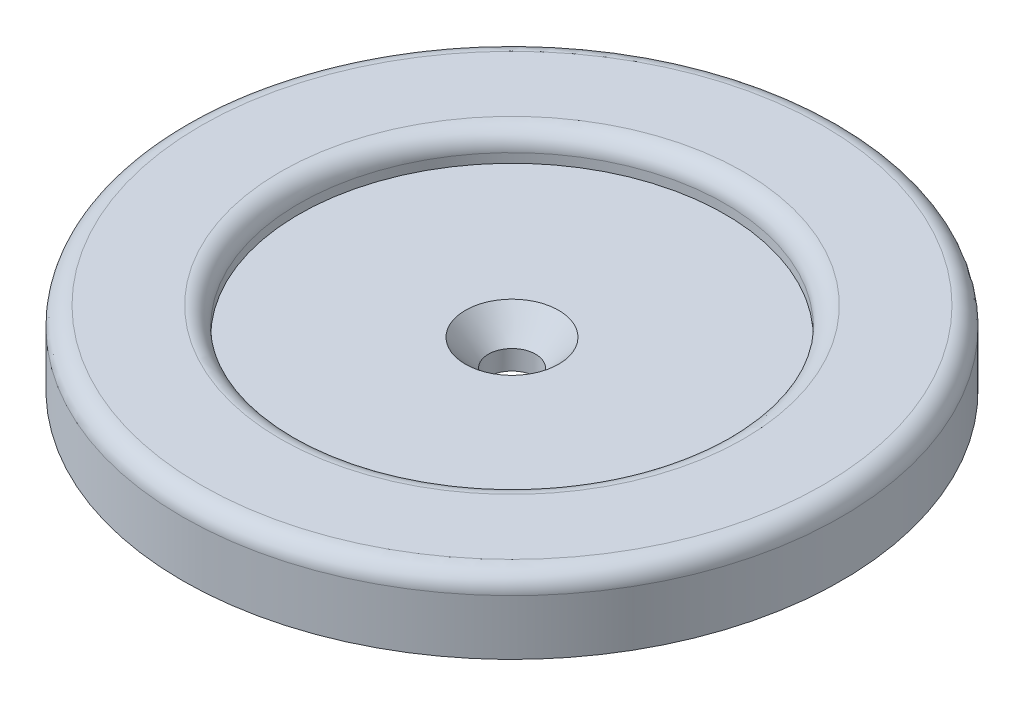
SolidWorks part; units mm, degrees
ref_plane "Front Plane" through (0, 0, 0) normal (0, 0, 1) x (1, 0, 0)
ref_plane "Top Plane" through (0, 0, 0) normal (0, 1, 0) x (1, 0, 0)
ref_plane "Right Plane" through (0, 0, 0) normal (1, 0, 0) x (0, 0, -1)
sketch "Sketch1" plane through (0, 0, 0) normal (0, 1, 0) x (1, 0, 0)
  circle A0 centre (0, 0) radius 20.066 construction
  circle A1 centre (0, 0) radius 45.466
  dimension "D1" = 25.4
extrude "Boss-Extrude1" add sketch "Sketch1" along normal blind 25.4
sketch "Sketch3" plane through (0, 0, 0) normal (0, -1, 0) x (1, 0, 0)
  circle A0 centre (0, 0) radius 20.32
hole_wizard "CSK for 1/4 Flat Head Machine Screw1" positions "Sketch6" profile "Sketch7" countersink size "1/4" standard "ANSI Inch"
sketch "Sketch6" plane through (0, 25.4, 0) normal (0, 1, 0) x (1, 0, 0)
  point P0 (0, 0)
sketch "Sketch7" plane through (0, 25.4, 0) normal (1, 0, 0) x (0, 0, 1)
  line L0 (0, 0) -> (0, 27.3611)
  line L1 (0, 27.3611) -> (3.2639, 25.4)
  line L2 (3.2639, 25.4) -> (3.2639, 3.6524)
  line L3 (3.2639, 3.6524) -> (6.4389, 0)
  line L5 (6.4389, 0) -> (0, 0)
  line L6 (-3.2639, 3.6524) -> (-6.4389, 0) construction
  line L10 (0, 27.3611) -> (-3.2639, 25.4) construction
  line L11 (0, -6.35) -> (0, 107.95) construction
  dimension "Hole Dia." = 6.5278
  dimension "Hole Depth" = 25.4
  dimension "Near C'Sink Dia." = 12.8778
  dimension "Near C'Sink Angle" = 82
  dimension "Drill Angle" = 118
sketch "Sketch9" plane through (0, 0, 0) normal (0, -1, 0) x (1, 0, 0)
  circle A0 centre (0, 0) radius 53.0319
extrude "Cut-Extrude3" cut sketch "Sketch9" against normal blind 12.7
sketch "Sketch11" plane through (0, 12.7, 0) normal (0, -1, 0) x (1, 0, 0)
  circle A0 centre (0, 0) radius 48.964
extrude "Cut-Extrude4" cut sketch "Sketch11" against normal blind 6.35
sketch "Sketch13" plane through (0, 25.4, 0) normal (0, 1, 0) x (1, 0, 0)
  circle A0 centre (0, 0) radius 29.3982
  circle A1 centre (0, 0) radius 45.466
extrude "Boss-Extrude2" add sketch "Sketch13" along normal blind 3.81
sketch "Sketch12" plane through (0, 19.05, 0) normal (0, -1, 0) x (1, 0, 0)
  circle A0 centre (0, 0) radius 38.3099 construction
  circle A1 centre (0, 38.3099) radius 3.1309
  circle A2 centre (9.9153, 37.0045) radius 3.1309
  circle A3 centre (19.1549, 33.1773) radius 3.1309
  circle A4 centre (27.0892, 27.0892) radius 3.1309
  circle A5 centre (33.1773, 19.1549) radius 3.1309
  circle A6 centre (37.0045, 9.9153) radius 3.1309
  circle A7 centre (38.3099, 0) radius 3.1309
  circle A8 centre (37.0045, -9.9153) radius 3.1309
  circle A9 centre (33.1773, -19.1549) radius 3.1309
  circle A10 centre (27.0892, -27.0892) radius 3.1309
  circle A11 centre (19.1549, -33.1773) radius 3.1309
  circle A12 centre (9.9153, -37.0045) radius 3.1309
  circle A13 centre (0, -38.3099) radius 3.1309
  circle A14 centre (-9.9153, -37.0045) radius 3.1309
  circle A15 centre (-19.1549, -33.1773) radius 3.1309
  circle A16 centre (-27.0892, -27.0892) radius 3.1309
  circle A17 centre (-33.1773, -19.1549) radius 3.1309
  circle A18 centre (-37.0045, -9.9153) radius 3.1309
  circle A19 centre (-38.3099, 0) radius 3.1309
  circle A20 centre (-37.0045, 9.9153) radius 3.1309
  circle A21 centre (-33.1773, 19.1549) radius 3.1309
  circle A22 centre (-27.0892, 27.0892) radius 3.1309
  circle A23 centre (-19.1549, 33.1773) radius 3.1309
  circle A24 centre (-9.9153, 37.0045) radius 3.1309
  point P53 (0, 0)
  dimension "D1" = 24
extrude "Cut-Extrude5" cut sketch "Sketch12" against normal blind 6.35
fillet "Fillet1" radius 2.54 2 edges at (0, 29.21, 45.466) (0, 29.21, 29.3982)
